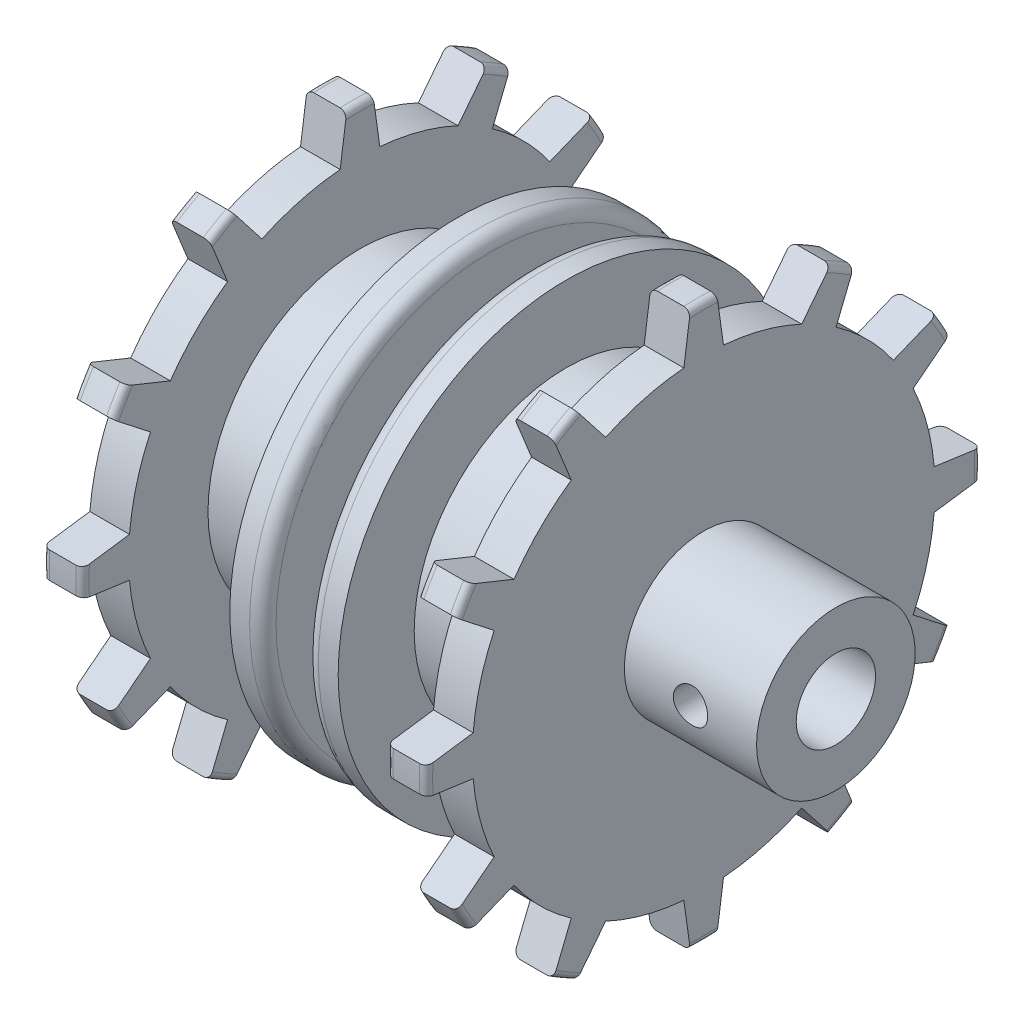
SolidWorks part; units mm, degrees
ref_plane "前视基准面" through (0, 0, 0) normal (0, 0, 1) x (1, 0, 0)
ref_plane "上视基准面" through (0, 0, 0) normal (0, 1, 0) x (1, 0, 0)
ref_plane "右视基准面" through (0, 0, 0) normal (1, 0, 0) x (0, 0, -1)
sketch "草图1" plane through (0, 0, 0) normal (0, 0, 1) x (1, 0, 0)
  line L0 (-17.7828, 0) -> (29.0933, 0) construction
  line L1 (2.6, 17.25) -> (4.1, 17.25)
  line L2 (1.6, 11.5) -> (1.6, 16.25)
  line L3 (-1.6, 11.5) -> (-1.6, 16.25)
  line L4 (4.1, 11.5) -> (4.1, 17.25)
  line L5 (-4.1, 11.5) -> (-4.1, 17.25)
  line L6 (-4.1, 17.25) -> (-2.6, 17.25)
  line L7 (1.6, 0) -> (1.6, 17.25) construction
  line L8 (-1.6, 0) -> (-1.6, 17.25) construction
  line L9 (14.5, 6) -> (14.5, 20.5)
  line L10 (4.1, 11.5) -> (11.5, 11.5)
  line L11 (24.5, 3) -> (10.5, 3)
  line L12 (11.5, 11.5) -> (11.5, 20.5)
  line L13 (-4.1, 0) -> (-4.1, 17.25) construction
  line L14 (-11.5, 11.5) -> (-4.1, 11.5)
  line L15 (-11.5, 11.5) -> (-11.5, 20.5)
  line L16 (-14.5, 8.4) -> (-14.5, 20.5)
  line L17 (10.5, 3) -> (10.5, 1.5)
  line L18 (12, 21) -> (14, 21)
  line L19 (-14, 21) -> (-12, 21)
  line L20 (-1.6, 11.5) -> (1.6, 11.5)
  line L21 (10.5, 1.5) -> (-2.5, 1.5)
  line L22 (14.5, 6) -> (24.5, 6)
  line L23 (4.1, 0) -> (4.1, 17.25) construction
  line L24 (24.5, 3) -> (24.5, 6)
  line L25 (-2.5, 1.5) -> (-2.5, 8.4)
  line L26 (-2.5, 8.4) -> (-14.5, 8.4)
  arc A0 (1.6, 16.25) -> (2.6, 17.25) centre (2.6, 16.25) cw
  arc A1 (-1.6, 16.25) -> (-2.6, 17.25) centre (-2.6, 16.25) ccw
  arc A2 (-11.5, 20.5) -> (-12, 21) centre (-12, 20.5) ccw
  arc A3 (-14.5, 20.5) -> (-14, 21) centre (-14, 20.5) cw
  arc A4 (14.5, 20.5) -> (14, 21) centre (14, 20.5) ccw
  arc A5 (11.5, 20.5) -> (12, 21) centre (12, 20.5) cw
  point P17 (-1.6, 17.25)
  point P27 (32.8982, 0)
  point P32 (0, 0)
  point P35 (0, 6)
  point P36 (32.8982, 6)
  point P49 (11.5, 21)
  dimension "D4" = 1
  dimension "D8" = 0.5
  dimension "D2" = 14
  dimension "D3" = 8.4
  dimension "D9" = 3.2
  dimension "D13" = 1.5
  dimension "D14" = 10
  dimension "D11" = 7.4
  dimension "D12" = 7.4
  dimension "D5" = 12
  dimension "D6" = 2.5
  dimension "D7" = 2.5
revolve "旋转1" add sketch "草图1" angle 360 about L0
sketch "草图2" plane through (0, 0, 0) normal (0, 0, 1) x (1, 0, 0)
  line L1 (14.5, -6) -> (14.5, 6) construction
  circle A1 centre (19.5, 0) radius 1.3
  dimension "D1" = 5
  dimension "D2" = 2.6
extrude "切除-拉伸1" cut sketch "草图2" along normal blind 10
sketch "草图3" plane through (14.5, 0, 0) normal (1, 0, 0) x (0, 0, -1)
  line L0 (14.3497, 10.0168) -> (17.6641, 11.357)
  line L1 (10.0168, 14.3497) -> (11.366, 17.6865)
  line L2 (17.4356, 1.5) -> (20.9761, 1.0034)
  line L3 (15.8497, 7.4188) -> (18.6865, 9.634)
  line L4 (15.8497, -7.4188) -> (18.6675, -9.6191)
  line L5 (17.4356, -1.5) -> (21, -1)
  line L6 (10.0168, -14.3497) -> (11.357, -17.6641)
  line L7 (14.3497, -10.0168) -> (17.6865, -11.366)
  line L8 (1.5, -17.4356) -> (1.0034, -20.9761)
  line L9 (7.4188, -15.8497) -> (9.634, -18.6865)
  line L10 (-7.4188, -15.8497) -> (-9.6191, -18.6675)
  line L11 (-1.5, -17.4356) -> (-1, -21)
  line L12 (-14.3497, -10.0168) -> (-17.6641, -11.357)
  line L13 (-10.0168, -14.3497) -> (-11.366, -17.6865)
  line L14 (-17.4356, -1.5) -> (-20.9761, -1.0034)
  line L15 (-15.8497, -7.4188) -> (-18.6865, -9.634)
  line L16 (-15.8497, 7.4188) -> (-18.6675, 9.6191)
  line L17 (-17.4356, 1.5) -> (-21, 1)
  line L18 (-10.0168, 14.3497) -> (-11.357, 17.6641)
  line L19 (7.4188, 15.8497) -> (9.6191, 18.6675)
  line L20 (-14.3497, 10.0168) -> (-17.6865, 11.366)
  line L22 (-1.5, 17.4356) -> (-1.0034, 20.9761)
  line L23 (-7.4188, 15.8497) -> (-9.634, 18.6865)
  line L29 (1.5, 17.4356) -> (1, 21)
  arc A0 (1, 21) -> (9.6191, 18.6675) centre (0.365, 1.5626) cw
  arc A1 (11.366, 17.6865) -> (17.6641, 11.357) centre (1.0974, 1.1708) cw
  arc A2 (10.0168, 14.3497) -> (14.3497, 10.0168) centre (0, 0) cw
  arc A3 (18.6865, 9.634) -> (20.9761, 1.0034) centre (1.5358, 0.4652) cw
  arc A4 (1.5, 17.4356) -> (7.4188, 15.8497) centre (0, 0) cw
  arc A5 (15.8497, 7.4188) -> (17.4356, 1.5) centre (0, 0) cw
  arc A6 (21, -1) -> (18.6675, -9.6191) centre (1.5626, -0.365) cw
  arc A7 (17.4356, -1.5) -> (15.8497, -7.4188) centre (0, 0) cw
  arc A8 (17.6865, -11.366) -> (11.357, -17.6641) centre (1.1708, -1.0974) cw
  arc A9 (14.3497, -10.0168) -> (10.0168, -14.3497) centre (0, 0) cw
  arc A10 (9.634, -18.6865) -> (1.0034, -20.9761) centre (0.4652, -1.5358) cw
  arc A11 (7.4188, -15.8497) -> (1.5, -17.4356) centre (0, 0) cw
  arc A12 (-1, -21) -> (-9.6191, -18.6675) centre (-0.365, -1.5626) cw
  arc A13 (-1.5, -17.4356) -> (-7.4188, -15.8497) centre (0, 0) cw
  arc A14 (-11.366, -17.6865) -> (-17.6641, -11.357) centre (-1.0974, -1.1708) cw
  arc A15 (-10.0168, -14.3497) -> (-14.3497, -10.0168) centre (0, 0) cw
  arc A16 (-18.6865, -9.634) -> (-20.9761, -1.0034) centre (-1.5358, -0.4652) cw
  arc A17 (-15.8497, -7.4188) -> (-17.4356, -1.5) centre (0, 0) cw
  arc A18 (-21, 1) -> (-18.6675, 9.6191) centre (-1.5626, 0.365) cw
  arc A19 (-17.4356, 1.5) -> (-15.8497, 7.4188) centre (0, 0) cw
  arc A20 (-17.6865, 11.366) -> (-11.357, 17.6641) centre (-1.1708, 1.0974) cw
  arc A21 (-14.3497, 10.0168) -> (-10.0168, 14.3497) centre (0, 0) cw
  arc A22 (-9.634, 18.6865) -> (-1.0034, 20.9761) centre (-0.4652, 1.5358) cw
  arc A23 (-7.4188, 15.8497) -> (-1.5, 17.4356) centre (0, 0) cw
  point P0 (0, 0)
  point P4 (0, 21)
  point P21 (10.5, 18.1865)
  point P22 (1.5, 5.5981)
  point P23 (1.5, 21)
  point P24 (9.634, 19.8209)
  point P25 (1, 3.7321)
  point P26 (9.634, 18.6865)
  point P83 (0, 0)
  dimension "D1" = 12
extrude "切除-拉伸2" cut sketch "草图3" against normal blind 30
